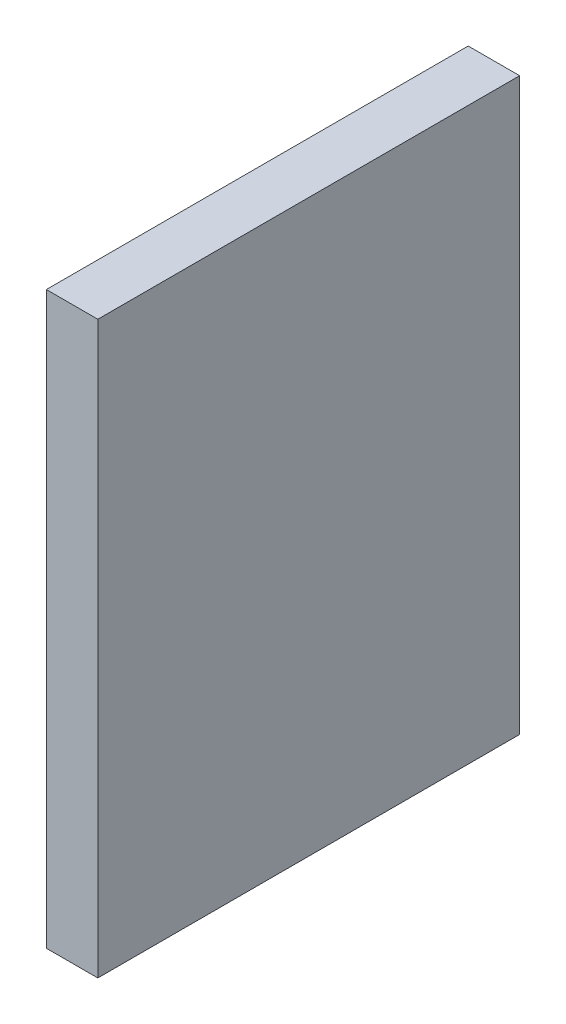
SolidWorks part; units mm, degrees
ref_plane "Alzado" through (0, 0, 0) normal (0, 0, 1) x (1, 0, 0)
ref_plane "Planta" through (0, 0, 0) normal (0, 1, 0) x (1, 0, 0)
ref_plane "Vista lateral" through (0, 0, 0) normal (1, 0, 0) x (0, 0, -1)
sketch "Croquis1" plane through (0, 0, 0) normal (1, 0, 0) x (0, 0, -1)
  line L0 (-1.0905, -21.408) -> (-1.0905, 11.8623)
  line L1 (-1.0905, 11.8623) -> (-25.6905, 11.8623)
  line L2 (-25.6905, 11.8623) -> (-25.6905, -21.408)
  line L3 (-25.6905, -21.408) -> (-1.0905, -21.408)
extrude "Saliente-Extruir1" add sketch "Croquis1" along normal blind 3
